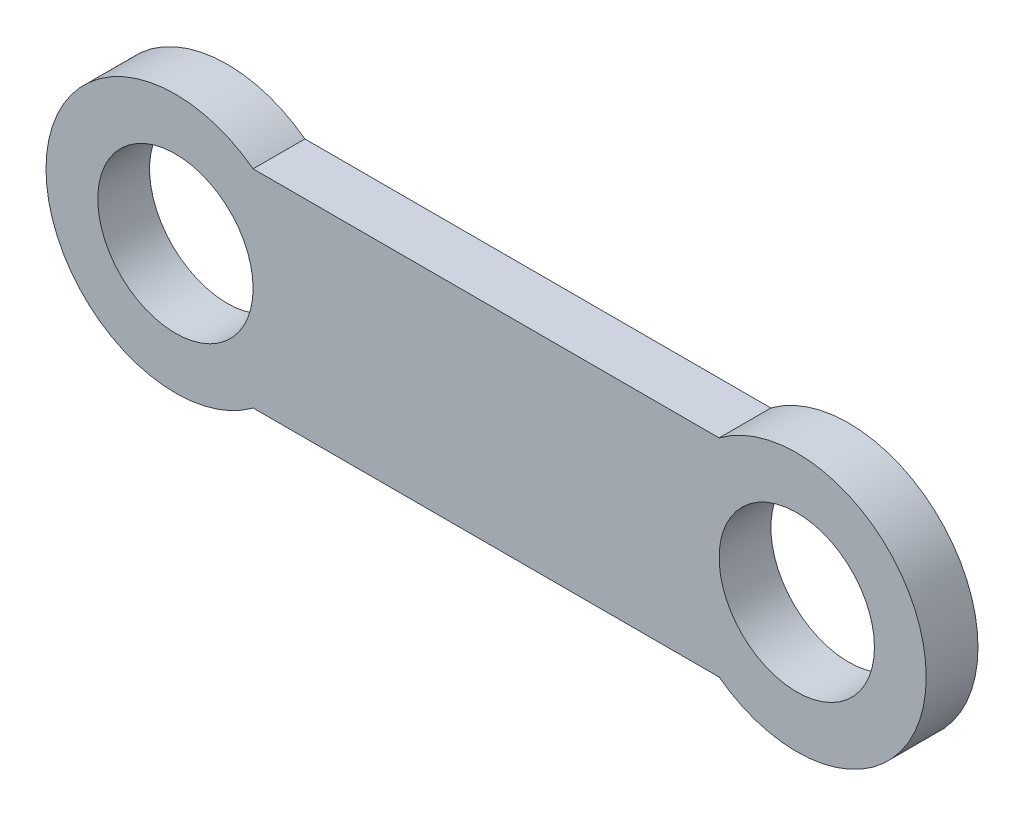
SolidWorks part; units mm, degrees
ref_plane "前视基准面" through (0, 0, 0) normal (0, 0, 1) x (1, 0, 0)
ref_plane "上视基准面" through (0, 0, 0) normal (0, 1, 0) x (1, 0, 0)
ref_plane "右视基准面" through (0, 0, 0) normal (1, 0, 0) x (0, 0, -1)
sketch "草图1" plane through (0, 0, 0) normal (0, 0, 1) x (1, 0, 0)
  line L1 (-4.5, 2) -> (4.5, 2)
  line L3 (-4.5, -2) -> (4.5, -2)
  arc A0 (4.5, -2) -> (4.5, 2) centre (6, 0) ccw
  arc A1 (-4.5, 2) -> (-4.5, -2) centre (-6, 0) ccw
  circle A2 centre (6, 0) radius 1.5
  circle A3 centre (-6, 0) radius 1.5
  point P0 (0, 0)
  dimension "D2" = 5
  dimension "D3" = 5
  dimension "D1" = 4
  dimension "D4" = 12
  dimension "D5" = 6
  dimension "D6" = 2
extrude "凸台-拉伸1" add sketch "草图1" along normal blind 1
